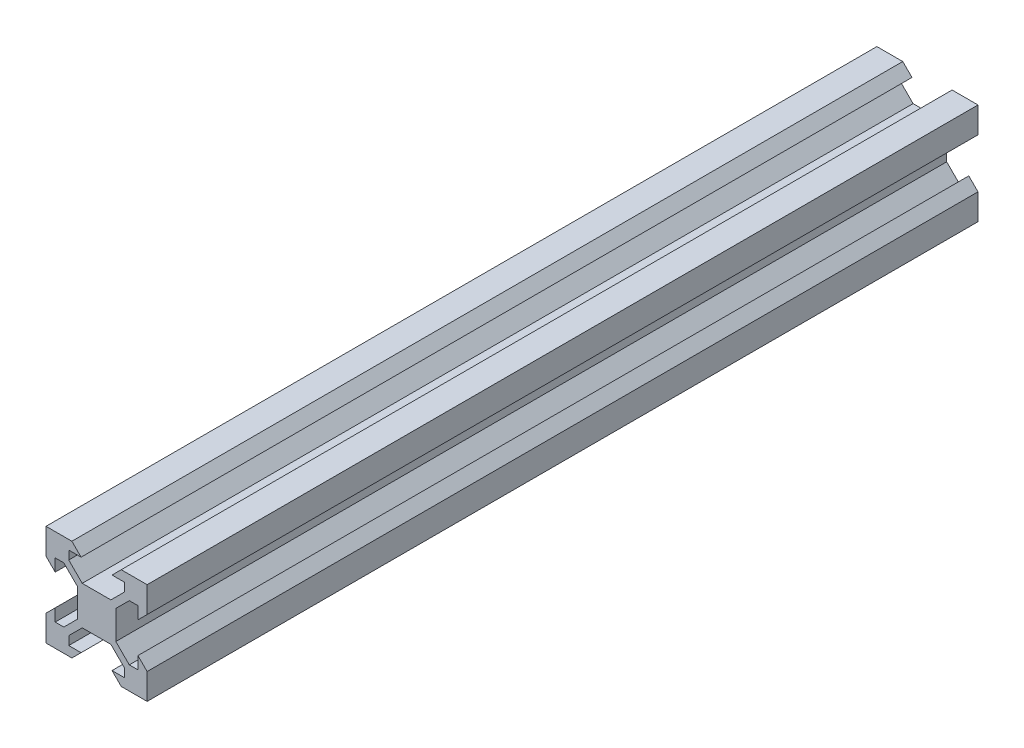
SolidWorks part; units mm, degrees
ref_plane "Front Plane" through (0, 0, 0) normal (0, 0, 1) x (1, 0, 0)
ref_plane "Top Plane" through (0, 0, 0) normal (0, 1, 0) x (1, 0, 0)
ref_plane "Right Plane" through (0, 0, 0) normal (1, 0, 0) x (0, 0, -1)
sketch "Sketch1" plane through (0, 0, 0) normal (0, 0, 1) x (1, 0, 0)
  line L1 (0, 0) -> (20, 0)
  line L2 (0, 0) -> (0, 20)
  line L3 (0, 20) -> (20, 20)
  line L4 (20, 0) -> (20, 20)
  line L5 (0, 0) -> (20, 20) construction
  line L6 (0, 20) -> (20, 0) construction
  point P4 (10, 10)
  dimension "D1" = 20
  dimension "D2" = 20
extrude "Boss-Extrude1" add sketch "Sketch1" along normal blind 164.34
sketch "Sketch2" plane through (0, 0, 164.34) normal (0, 0, 1) x (1, 0, 0)
  line L4 (0, 0) -> (20, 20) construction
  line L5 (4.5, 18.18) -> (6.94, 18.18)
  line L6 (4.5, 16.4758) -> (4.5, 18.18)
  line L15 (7.1658, 13.81) -> (4.5, 16.4758)
  line L17 (12.8342, 13.81) -> (7.1658, 13.81)
  line L27 (15.5, 16.4758) -> (12.8342, 13.81)
  line L29 (15.5, 18.18) -> (15.5, 16.4758)
  line L31 (13.06, 18.18) -> (15.5, 18.18)
  line L33 (14.88, 20) -> (5.12, 20)
  line L35 (6.94, 18.18) -> (5.12, 20)
  line L54 (14.88, 20) -> (13.06, 18.18)
  line L56 (14.88, 0) -> (13.06, 1.82)
  line L57 (6.94, 1.82) -> (5.12, 0)
  line L58 (14.88, 0) -> (5.12, 0)
  line L68 (13.06, 1.82) -> (15.5, 1.82)
  line L71 (15.5, 1.82) -> (15.5, 3.5242)
  line L81 (15.5, 3.5242) -> (12.8342, 6.19)
  line L82 (12.8342, 6.19) -> (7.1658, 6.19)
  line L83 (7.1658, 6.19) -> (4.5, 3.5242)
  line L84 (4.5, 3.5242) -> (4.5, 1.82)
  line L85 (4.5, 1.82) -> (6.94, 1.82)
  line L136 (20, 0) -> (10, 0) construction
  line L137 (0, 0) -> (20, 0) construction
  line L186 (1.82, 4.5) -> (1.82, 6.94)
  line L187 (3.5242, 4.5) -> (1.82, 4.5)
  line L188 (6.19, 7.1658) -> (3.5242, 4.5)
  line L189 (6.19, 12.8342) -> (6.19, 7.1658)
  line L190 (3.5242, 15.5) -> (6.19, 12.8342)
  line L191 (1.82, 15.5) -> (3.5242, 15.5)
  line L192 (1.82, 13.06) -> (1.82, 15.5)
  line L193 (0, 14.88) -> (0, 5.12)
  line L194 (1.82, 6.94) -> (0, 5.12)
  line L195 (0, 14.88) -> (1.82, 13.06)
  line L203 (20, 14.88) -> (18.18, 13.06)
  line L205 (18.18, 6.94) -> (20, 5.12)
  line L206 (20, 14.88) -> (20, 5.12)
  line L207 (18.18, 13.06) -> (18.18, 15.5)
  line L208 (18.18, 15.5) -> (16.4758, 15.5)
  line L209 (16.4758, 15.5) -> (13.81, 12.8342)
  line L210 (13.81, 12.8342) -> (13.81, 7.1658)
  line L211 (13.81, 7.1658) -> (16.4758, 4.5)
  line L212 (16.4758, 4.5) -> (18.18, 4.5)
  line L213 (18.18, 4.5) -> (18.18, 6.94)
extrude "Cut-Extrude1" cut sketch "Sketch2" against normal through all
